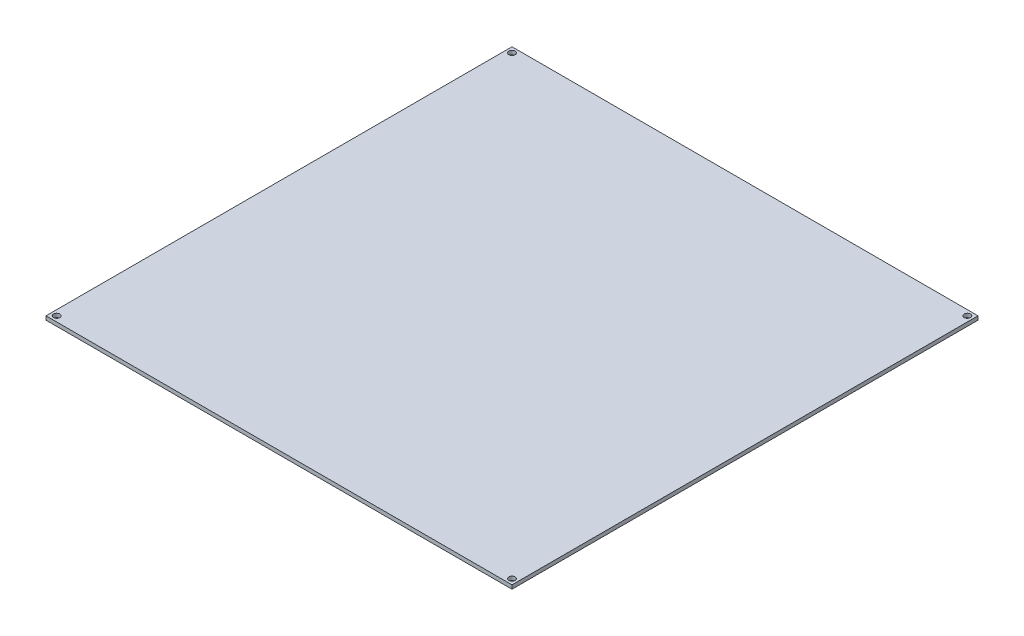
SolidWorks part; units mm, degrees
ref_plane "Front Plane" through (0, 0, 0) normal (0, 0, 1) x (1, 0, 0)
ref_plane "Top Plane" through (0, 0, 0) normal (0, 1, 0) x (1, 0, 0)
ref_plane "Right Plane" through (0, 0, 0) normal (1, 0, 0) x (0, 0, -1)
sketch "Sketch1" plane through (0, 0, 0) normal (0, 1, 0) x (1, 0, 0)
  line L0 (0, 0) -> (0, 107) construction
  line L1 (-107, 107) -> (107, 107)
  line L2 (-107, 107) -> (-107, -107)
  line L3 (-107, -107) -> (107, -107)
  line L4 (107, 107) -> (107, -107)
  line L5 (0, 0) -> (107, 0) construction
  line L6 (-106, 104.555) -> (-106, 107) construction
  line L7 (-104.555, 106) -> (-107, 106) construction
  circle A0 centre (-104.555, 104.555) radius 1.445
  circle A1 centre (104.555, 104.555) radius 1.445
  circle A2 centre (104.555, -104.555) radius 1.445
  circle A3 centre (-104.555, -104.555) radius 1.445
  dimension "D4" = 2.89
  dimension "D1" = 214
  dimension "D2" = 214
  dimension "D3" = 1
  dimension "D5" = 1
extrude "Boss-Extrude1" add sketch "Sketch1" along normal blind 1.75
